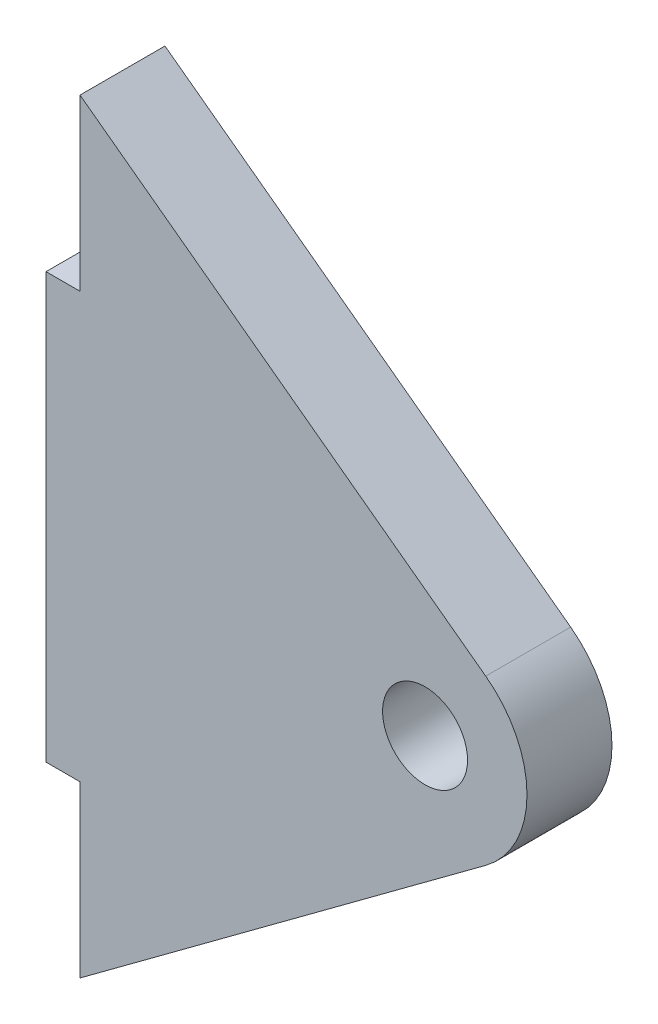
SolidWorks part; units mm, degrees
material "7075-O (SS)"
ref_plane "Płaszczyzna XY" through (0, 0, 0) normal (0, 0, 1) x (1, 0, 0)
ref_plane "Płaszczyzna XZ" through (0, 0, 0) normal (0, 1, 0) x (1, 0, 0)
ref_plane "Płaszczyzna YZ" through (0, 0, 0) normal (1, 0, 0) x (0, 0, -1)
sketch "Szkic1" plane through (0, 0, 0) normal (0, 0, 1) x (1, 0, 0)
  line L0 (190.4754, 224.5576) -> (190.4754, 234.5576)
  line L1 (190.4754, 234.5576) -> (214.3516, 216.8797)
  line L2 (214.3516, 207.2354) -> (190.4754, 189.5576)
  line L3 (190.4754, 189.5576) -> (190.4754, 199.5576)
  line L4 (188.4754, 199.5576) -> (190.4754, 199.5576)
  line L5 (190.4754, 199.5576) -> (190.4754, 224.5576)
  line L6 (190.4754, 224.5576) -> (188.4754, 224.5576)
  line L7 (188.4754, 224.5576) -> (188.4754, 199.5576)
  line L8 (188.4754, 199.5576) -> (190.4754, 199.5576)
  line L9 (190.4754, 199.5576) -> (190.4754, 224.5576)
  line L10 (190.4754, 224.5576) -> (188.4754, 224.5576)
  line L11 (188.4754, 224.5576) -> (188.4754, 199.5576)
  circle A0 centre (210.7813, 212.0576) radius 2.5
  arc A1 (214.3516, 216.8797) -> (214.3516, 207.2354) centre (210.7813, 212.0576) cw
  point P12 (220.8645, 212.0576)
  dimension "D6" = 5
  dimension "D7" = 6
  dimension "D2" = 10
  dimension "D3" = 10
  dimension "D4" = 22.5
  dimension "D5" = 22.5
  dimension "D1" = 0
extrude "Dodanie-wyciągnięcie1" add sketch "Szkic1" along normal blind 5 contours A1 L1 L0 L9 L3 L2 A0 | L10 L11 L8 L9
